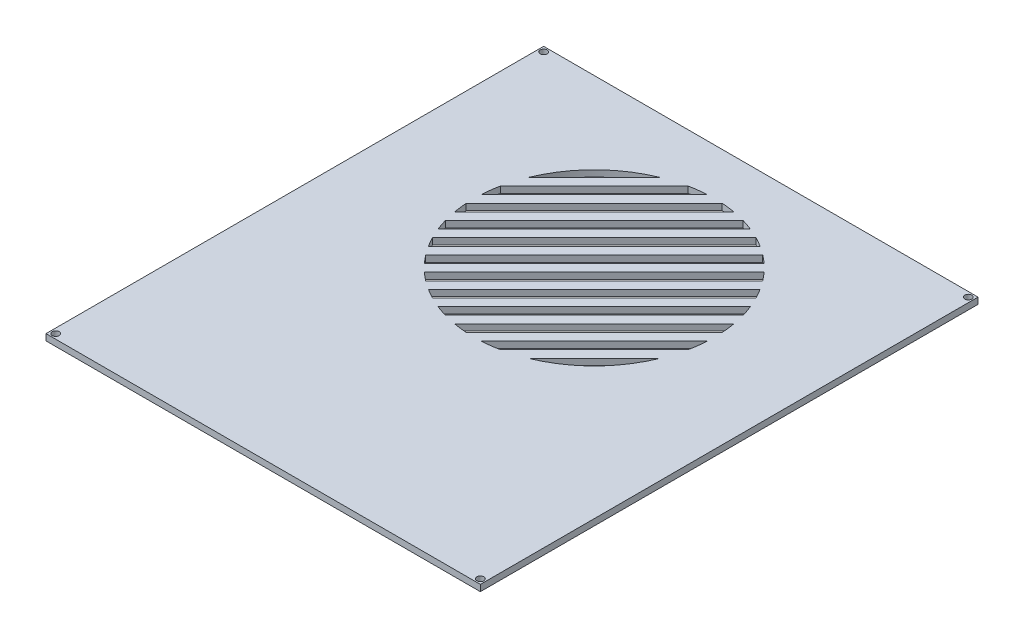
SolidWorks part; units mm, degrees
ref_plane "Ebene vorne" through (0, 0, 0) normal (0, 0, 1) x (1, 0, 0)
ref_plane "Ebene oben" through (0, 0, 0) normal (0, 1, 0) x (1, 0, 0)
ref_plane "Ebene rechts" through (0, 0, 0) normal (1, 0, 0) x (0, 0, -1)
sketch "Skizze1" plane through (0, 0, 0) normal (0, 1, 0) x (1, 0, 0)
  line L1 (-103, -118) -> (103, -118)
  line L2 (-103, -118) -> (-103, 118)
  line L3 (-103, 118) -> (103, 118)
  line L4 (103, -118) -> (103, 118)
  line L5 (-103, -118) -> (103, 118) construction
  line L6 (-103, 118) -> (103, -118) construction
  point P0 (0, 0)
  dimension "D1" = 206
  dimension "D2" = 236
extrude "Aufsatz-Linear austragen1" add sketch "Skizze1" along normal blind 3
sketch "Skizze2" plane through (0, 3, 0) normal (0, 1, 0) x (1, 0, 0)
  line L0 (0, -55) -> (0, 55) construction
  line L1 (-60, -17.464) -> (52.6857, 95.2217)
  line L2 (-60, -21) -> (60, -21) construction
  line L3 (-60, -21) -> (-60, 99) construction
  line L4 (-60, 99) -> (60, 99) construction
  line L5 (60, -21) -> (60, 99) construction
  line L6 (-60, -21) -> (60, 99) construction
  line L7 (-60, 99) -> (60, -21) construction
  line L8 (-60, -17.464) -> (-63.5355, -13.9285)
  line L9 (52.6857, 95.2217) -> (49.1502, 98.7573)
  line L10 (-63.5355, -13.9285) -> (49.1502, 98.7573)
  line L11 (-63.5355, -13.9285) -> (49.1502, 98.7573)
  line L12 (-63.5355, -13.9285) -> (-67.0711, -10.3929)
  line L13 (103, 118) -> (-103, 118) construction
  line L14 (-56.464, -21) -> (-60, -17.464)
  line L15 (-56.464, -21) -> (56.2217, 91.6857)
  line L16 (-60, -17.464) -> (52.6857, 95.2217)
  line L17 (56.2217, 91.6857) -> (52.6857, 95.2217)
  line L18 (-56.464, -21) -> (-52.9285, -24.5355)
  line L19 (-56.464, -21) -> (56.1996, 91.6636)
  line L20 (-52.9285, -24.5355) -> (59.7351, 88.128)
  line L21 (56.1996, 91.6636) -> (59.7351, 88.128)
  line L22 (49.1502, 98.7573) -> (45.6147, 102.2928)
  line L23 (-67.0711, -10.3929) -> (45.6147, 102.2928)
  line L28 (-67.0711, -10.3929) -> (45.6147, 102.2928)
  line L29 (-67.0711, -10.3929) -> (-70.6066, -6.8574)
  line L30 (45.6147, 102.2928) -> (42.0791, 105.8283)
  line L31 (-70.6066, -6.8574) -> (42.0791, 105.8283)
  line L32 (-70.6066, -6.8574) -> (42.0791, 105.8283)
  line L33 (-70.6066, -6.8574) -> (-74.1421, -3.3219)
  line L34 (42.0791, 105.8283) -> (38.5436, 109.3639)
  line L35 (-74.1421, -3.3219) -> (38.5436, 109.3639)
  line L36 (-74.1421, -3.3219) -> (33.1649, 103.9851)
  line L37 (-74.1421, -3.3219) -> (-77.6777, 0.2137)
  line L38 (33.1649, 103.9851) -> (29.6293, 107.5207)
  line L39 (-77.6777, 0.2137) -> (29.6293, 107.5207)
  line L40 (-77.6777, 0.2137) -> (26.5429, 104.4342)
  line L41 (-77.6777, 0.2137) -> (-81.2132, 3.7492)
  line L42 (26.5429, 104.4342) -> (23.0073, 107.9697)
  line L43 (-81.2132, 3.7492) -> (23.0073, 107.9697)
  line L44 (-81.2132, 3.7492) -> (16.4647, 101.4271)
  line L45 (-81.2132, 3.7492) -> (-84.7487, 7.2847)
  line L46 (16.4647, 101.4271) -> (12.9291, 104.9626)
  line L47 (-84.7487, 7.2847) -> (12.9291, 104.9626)
  line L48 (-84.7487, 7.2847) -> (8.5814, 100.6148)
  line L49 (-84.7487, 7.2847) -> (-88.2843, 10.8203)
  line L50 (8.5814, 100.6148) -> (5.0458, 104.1504)
  line L51 (-88.2843, 10.8203) -> (5.0458, 104.1504)
  line L52 (-78.0445, 21.0601) -> (2.1056, 101.2102)
  line L53 (-78.0445, 21.0601) -> (-81.58, 24.5956)
  line L54 (2.1056, 101.2102) -> (-1.4299, 104.7457)
  line L55 (-81.58, 24.5956) -> (-1.4299, 104.7457)
  line L56 (-78.0445, 28.1312) -> (-4.9654, 101.2102)
  line L57 (-78.0445, 28.1312) -> (-81.58, 31.6667)
  line L58 (-4.9654, 101.2102) -> (-8.501, 104.7457)
  line L59 (-81.58, 31.6667) -> (-8.501, 104.7457)
  line L60 (-52.9285, -24.5355) -> (59.7351, 88.128)
  line L61 (-52.9285, -24.5355) -> (-49.3929, -28.0711)
  line L62 (59.7351, 88.128) -> (63.2706, 84.5925)
  line L63 (-49.3929, -28.0711) -> (63.2706, 84.5925)
  line L64 (-49.3929, -28.0711) -> (63.2706, 84.5925)
  line L65 (-49.3929, -28.0711) -> (-45.8574, -31.6066)
  line L66 (63.2706, 84.5925) -> (66.8062, 81.057)
  line L67 (-45.8574, -31.6066) -> (66.8062, 81.057)
  line L68 (-45.8574, -31.6066) -> (66.8062, 81.057)
  line L69 (-45.8574, -31.6066) -> (-42.3219, -35.1421)
  line L70 (66.8062, 81.057) -> (70.3417, 77.5214)
  line L71 (-42.3219, -35.1421) -> (70.3417, 77.5214)
  line L72 (-42.3219, -35.1421) -> (65.0384, 72.2181)
  line L73 (-42.3219, -35.1421) -> (-38.7863, -38.6777)
  line L74 (65.0384, 72.2181) -> (68.5739, 68.6826)
  line L75 (-38.7863, -38.6777) -> (68.5739, 68.6826)
  line L76 (-38.7863, -38.6777) -> (65.0384, 65.1471)
  line L77 (-38.7863, -38.6777) -> (-35.2508, -42.2132)
  line L78 (65.0384, 65.1471) -> (68.5739, 61.6115)
  line L79 (-35.2508, -42.2132) -> (68.5739, 61.6115)
  line L80 (-35.2508, -42.2132) -> (65.0384, 58.076)
  line L81 (-35.2508, -42.2132) -> (-31.7153, -45.7487)
  line L82 (65.0384, 58.076) -> (68.5739, 54.5405)
  line L83 (-31.7153, -45.7487) -> (68.5739, 54.5405)
  line L84 (-31.7153, -45.7487) -> (64.4611, 50.4277)
  line L85 (-31.7153, -45.7487) -> (-28.1797, -49.2843)
  line L86 (64.4611, 50.4277) -> (67.9967, 46.8921)
  line L87 (-28.1797, -49.2843) -> (67.9967, 46.8921)
  line L88 (-23.4039, -44.5085) -> (67.9967, 46.8921)
  line L89 (-23.4039, -44.5085) -> (-19.8684, -48.044)
  line L90 (67.9967, 46.8921) -> (71.5322, 43.3566)
  line L91 (-19.8684, -48.044) -> (71.5322, 43.3566)
  line L92 (-19.8684, -48.044) -> (71.5322, 43.3566)
  line L93 (-19.8684, -48.044) -> (-16.3329, -51.5795)
  line L94 (71.5322, 43.3566) -> (75.0677, 39.8211)
  line L95 (-16.3329, -51.5795) -> (75.0677, 39.8211)
  circle A1 centre (0, 39) radius 57
  point P2 (0, 39)
  dimension "D4" = 114
  dimension "D1" = 120
  dimension "D2" = 120
  dimension "D3" = 19
  dimension "D5" = 3.536
  dimension "D6" = 3.536
  dimension "D7" = 5
  dimension "D8" = 5
  dimension "D9" = 5
  dimension "D10" = 5
  dimension "D11" = 5
  dimension "D12" = 5
  dimension "D13" = 5
  dimension "D14" = 5
  dimension "D15" = 5
  dimension "D16" = 5
  dimension "D17" = 5
  dimension "D18" = 5
  dimension "D19" = 5
  dimension "D20" = 5
  dimension "D21" = 5
  dimension "D22" = 5
  dimension "D23" = 5
  dimension "D24" = 5
  dimension "D25" = 5
  dimension "D26" = 5
extrude "Schnitt-Linear austragen2" cut sketch "Skizze2" against normal blind 3 contours L59 A1 | L52 A1 L56 | L44 A1 L48 | L36 A1 L40 | L28 A1 L32 | L16 A1 L11 | L60 A1 L19 | L68 A1 L64 | L76 A1 L72 | L84 A1 L80 | L88 A1 L92 | L95 A1
sketch "Skizze3" plane through (0, 3, 0) normal (0, 1, 0) x (1, 0, 0)
  line L0 (-103, 118) -> (-103, -118) construction
  line L1 (103, 118) -> (-103, 118) construction
  line L2 (103, -118) -> (103, 118) construction
  line L3 (-103, -118) -> (103, -118) construction
  circle A0 centre (-100.7, 115.7) radius 1.65
  circle A1 centre (100.7, 115.7) radius 1.65
  circle A2 centre (100.7, -115.7) radius 1.65
  circle A3 centre (-100.7, -115.7) radius 1.65
  dimension "D2" = 2.3
  dimension "D5" = 3.3
  dimension "D8" = 3.3
  dimension "D9" = 3.3
  dimension "D1" = 2.3
  dimension "D3" = 2.3
  dimension "D4" = 2.3
  dimension "D6" = 2.3
  dimension "D7" = 2.3
  dimension "D10" = 2.3
extrude "Schnitt-Linear austragen3" cut sketch "Skizze3" against normal blind 3
